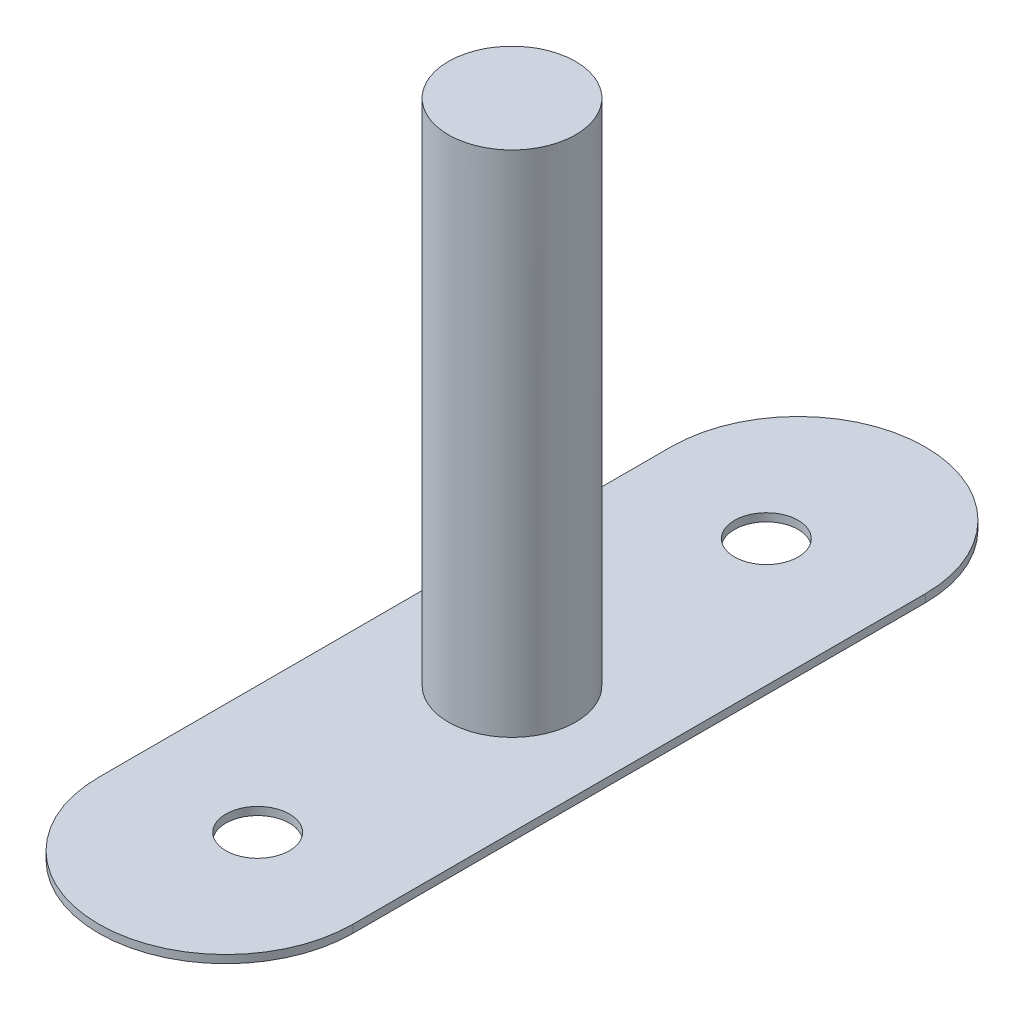
SolidWorks part; units mm, degrees
ref_plane "Front Plane" through (0, 0, 0) normal (0, 0, 1) x (1, 0, 0)
ref_plane "Top Plane" through (0, 0, 0) normal (0, 1, 0) x (1, 0, 0)
ref_plane "Right Plane" through (0, 0, 0) normal (1, 0, 0) x (0, 0, -1)
sketch "Sketch1" plane through (0, 0, 0) normal (0, 1, 0) x (1, 0, 0)
  line L0 (-12.7, -28.575) -> (-12.7, 28.575)
  line L1 (12.7, 28.575) -> (12.7, -28.575)
  line L2 (-12.7, 0) -> (12.7, 0) construction
  line L3 (0, 41.275) -> (0, -41.275) construction
  arc A0 (-12.7, 28.575) -> (12.7, 28.575) centre (0, 28.575) cw
  arc A1 (-12.7, -28.575) -> (12.7, -28.575) centre (0, -28.575) ccw
  dimension "D2" = 12.7
  dimension "D1" = 82.55
extrude "Boss-Extrude1" add sketch "Sketch1" along normal blind 0.7937
hole_wizard "CBORE for #4 Button Head Cap Screw1" positions "Sketch5" profile "Sketch4" counterbore size "#4" standard "Ansi Inch" end condition through all
sketch "Sketch5" plane through (0, 0.7937, 0) normal (0, 1, 0) x (-1, 0, 0)
  line L0 (0, 0) -> (16.1552, 0) construction
  point P0 (0, 25.4)
  point P9 (0, -25.4)
  dimension "D1" = 50.8
sketch "Sketch4" plane through (0, 0.7937, 25.4) normal (1, 0, 0) x (0, 0, 1)
  line L0 (0, 0) -> (0, 0.7938)
  line L1 (0, 0.7938) -> (1.632, 0.7938)
  line L3 (1.632, 0.7938) -> (1.632, 1.4986)
  line L4 (1.632, 1.4986) -> (3.175, 1.4986)
  line L5 (3.175, 1.4986) -> (3.175, 0)
  line L7 (3.175, 0) -> (0, 0)
  line L11 (0, -6.35) -> (0, 107.95) construction
  dimension "Thru Hole Dia." = 3.2639
  dimension "Thru Hole Depth" = 0.7937
  dimension "C'Bore Dia." = 6.35
  dimension "C'Bore Depth" = 1.4986
sketch "Sketch6" plane through (0, 0.7937, 0) normal (0, 1, 0) x (1, 0, 0)
  circle A0 centre (0, 0) radius 6.35
  point P0 (0, 0)
  dimension "D1" = 12.7
extrude "Boss-Extrude2" add sketch "Sketch6" along normal blind 50.8
